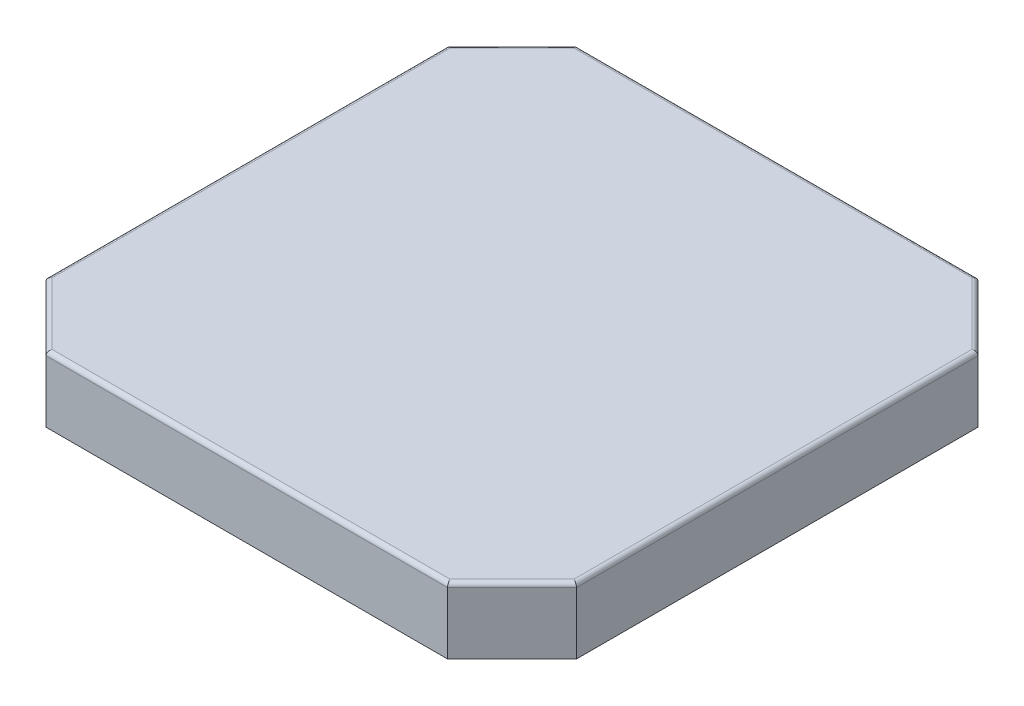
SolidWorks part; units mm, degrees
ref_plane "Plan de face" through (0, 0, 0) normal (0, 0, 1) x (1, 0, 0)
ref_plane "Plan de dessus" through (0, 0, 0) normal (0, 1, 0) x (1, 0, 0)
ref_plane "Plan de droite" through (0, 0, 0) normal (1, 0, 0) x (0, 0, -1)
sketch "Esquisse1" plane through (0, 0, 0) normal (0, 1, 0) x (1, 0, 0)
  line L1 (0, 0) -> (24.7, 0)
  line L2 (0, 0) -> (0, 24.7)
  line L3 (0, 24.7) -> (24.7, 24.7)
  line L4 (24.7, 0) -> (24.7, 24.7)
  dimension "D1" = 24.7
  dimension "D2" = 24.7
extrude "Boss.-Extru.1" add sketch "Esquisse1" along normal blind 3.08
chamfer "Chanfrein1" distance 3 angle 45 4 edges at (0, 1.54, -24.7) (24.7, 1.54, -24.7) (24.7, 1.54, 0) (0, 1.54, 0)
fillet "Congé1" radius 0.2 8 edges at (0, 3.08, -12.35) (1.5, 3.08, -1.5) (12.35, 3.08, 0) (23.2, 3.08, -1.5) (24.7, 3.08, -12.35) (23.2, 3.08, -23.2) (12.35, 3.08, -24.7) (1.5, 3.08, -23.2)
sketch "Esquisse2" plane through (0, 0, -24.7) normal (0, 0, -1) x (-1, 0, 0)
  line L0 (-21.7, 0) -> (-3, 0) construction
  line L1 (-15.35, 0) -> (-9.35, 0)
  line L2 (-15.35, 0) -> (-15.35, 2.88)
  line L3 (-15.35, 2.88) -> (-9.35, 2.88)
  line L4 (-9.35, 0) -> (-9.35, 2.88)
  line L5 (-3, 2.88) -> (-21.7, 2.88) construction
  line L6 (-21.7, 2.88) -> (-21.7, 0) construction
  line L7 (-3, 0) -> (-3, 2.88) construction
  point P8 (-21.7, 1.44)
  dimension "D1" = 6
  dimension "D2" = 6.35
  dimension "D3" = 6.35
extrude "Enlèv. mat.-Extru.1" cut sketch "Esquisse2" against normal blind 22.08
sketch "Esquisse3" plane through (0, 0, 0) normal (0, -1, 0) x (1, 0, 0)
  line L6 (3.1243, -24.4) -> (21.5757, -24.4)
  line L7 (24.4, -3.1243) -> (24.4, -21.5757)
  line L8 (3.1243, -0.3) -> (21.5757, -0.3)
  line L9 (0.3, -3.1243) -> (0.3, -21.5757)
  line L10 (3.1243, -0.3) -> (0.3, -3.1243)
  line L11 (3, 0) -> (0, -3) construction
  line L14 (24.4, -21.5757) -> (21.5757, -24.4)
  line L16 (3.1243, -24.4) -> (0.3, -21.5757)
  line L18 (21.7, -24.7) -> (24.7, -21.7) construction
  line L19 (0, -21.7) -> (3, -24.7) construction
  line L24 (21.5757, -0.3) -> (24.4, -3.1243)
  dimension "D2" = 0.3
  dimension "D4" = 0.3
  dimension "D5" = 0.3
extrude "Enlèv. mat.-Extru.2" cut sketch "Esquisse3" against normal up to surface (2.88 mm away) up to face at (12.35, 2.88, -13.66)
